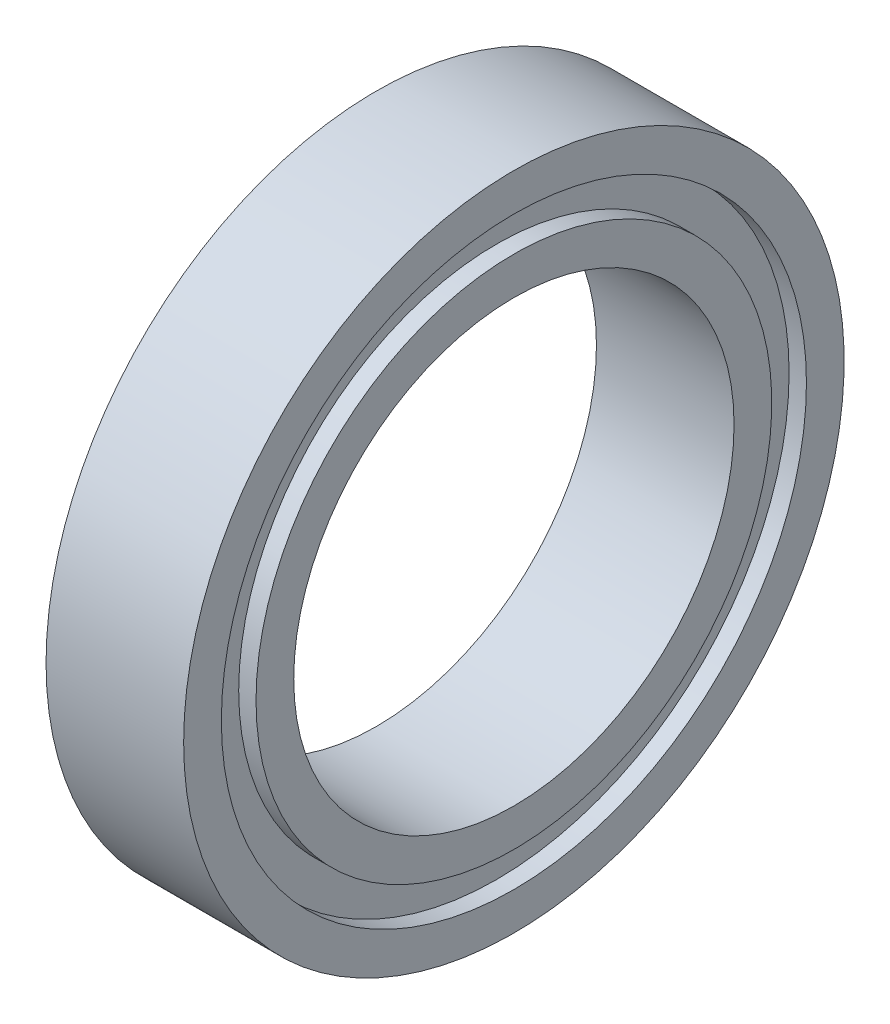
SolidWorks part; units mm, degrees
material "Plain Carbon Steel"
ref_plane "Front Plane" through (0, 0, 0) normal (0, 0, 1) x (1, 0, 0)
ref_plane "Top Plane" through (0, 0, 0) normal (0, 1, 0) x (1, 0, 0)
ref_plane "Right Plane" through (0, 0, 0) normal (1, 0, 0) x (0, 0, -1)
sketch "Sketch1" plane through (0, 0, 0) normal (0, 0, 1) x (1, 0, 0)
  line L0 (-1.9844, 7.4375) -> (-1.9844, 6.35)
  line L1 (-1.9844, 9.525) -> (1.9844, 9.525)
  line L2 (-1.9844, 9.525) -> (-1.9844, 8.4375)
  line L3 (-1.9844, 6.35) -> (1.9844, 6.35)
  line L4 (1.9844, 9.525) -> (1.9844, 8.4375)
  line L5 (-1.9844, 8.4375) -> (-1.4844, 8.4375)
  line L6 (1.9844, 7.4375) -> (1.9844, 6.35)
  line L7 (-1.9844, 7.4375) -> (-1.4844, 7.4375)
  line L8 (-1.4844, 8.4375) -> (-1.4844, 7.4375)
  line L9 (1.9844, 8.4375) -> (1.4844, 8.4375)
  line L10 (0, 0) -> (0, 9.525) construction
  line L11 (1.9844, 7.4375) -> (1.4844, 7.4375)
  line L12 (1.4844, 8.4375) -> (1.4844, 7.4375)
  line L13 (-6.8391, 0) -> (9.9159, 0) construction
  dimension "D1" = 12.7
  dimension "D2" = 19.05
  dimension "D3" = 3.9688
  dimension "D4" = 0.5
  dimension "D5" = 1
revolve "Revolve1" add sketch "Sketch1" angle 360 about L13
